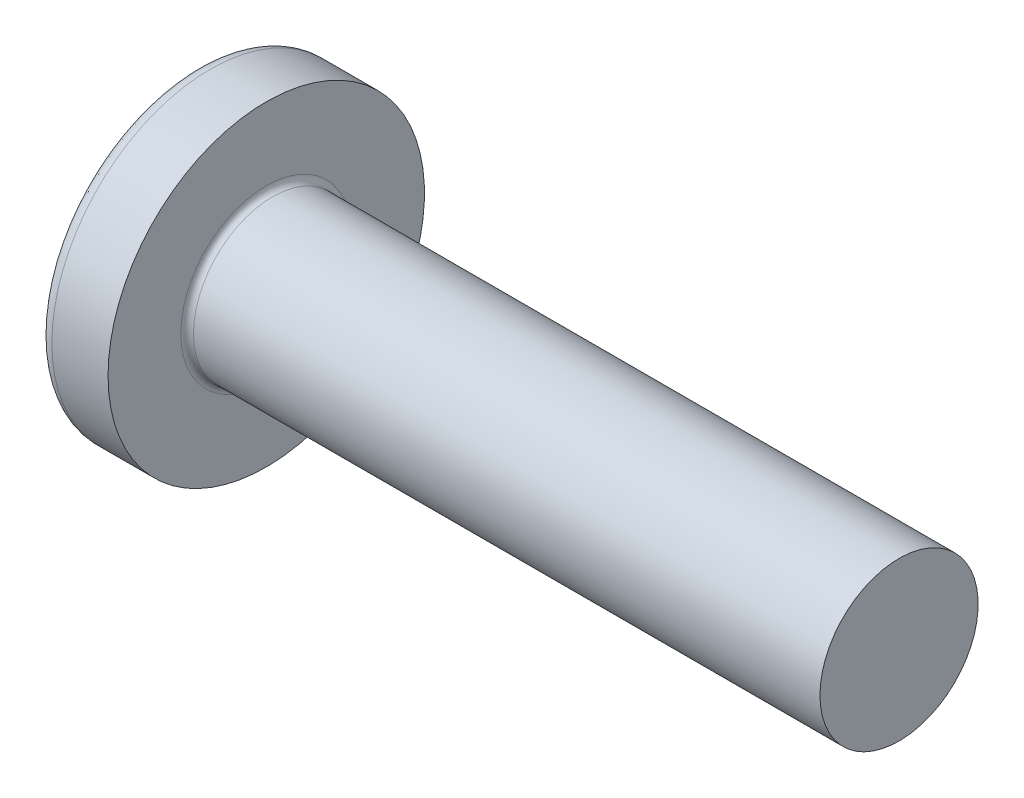
SolidWorks part; units mm, degrees
ref_plane "Plane1" through (0, 0, 0) normal (0, 0, 1) x (1, 0, 0)
ref_plane "Plane2" through (0, 0, 0) normal (0, 1, 0) x (1, 0, 0)
ref_plane "Plane3" through (0, 0, 0) normal (1, 0, 0) x (0, 0, -1)
sketch "BodySke" plane through (0, 0, 0) normal (0, 0, 1) x (1, 0, 0)
  line L0 (7.5, 5) -> (7.5, 10)
  line L1 (8.25, 6.35) -> (8.25, -3.175) construction
  line L2 (-25.4, 0) -> (127, 0) construction
  line L3 (47.5, 0) -> (0, 0)
  line L4 (7.5, 5) -> (47.5, 5)
  line L5 (47.5, 5) -> (47.5, 0)
  line L6 (3.9501, 10) -> (7.5, 10)
  line L8 (7.5, 6.35) -> (7.5, -3.175) construction
  arc A0 (3.2319, 9.6424) -> (0, 0) centre (16, 0) ccw
  arc A2 (3.2319, 9.6424) -> (3.9501, 10) centre (3.9501, 9.1) cw
  dimension "Head_fillet_rad" = 0.9
  dimension "Head_crown_rad" = 16
  dimension "Head_ht" = 7.5
  dimension "Diameter" = 10
  dimension "Length" = 40
  dimension "Head_dia" = 20
  dimension "Advance" = 1.5
  dimension "Thread_nom" = 40
revolve "Base-Revolve" add sketch "BodySke"
cosmetic thread "ThreadCosmetic"
fillet "Fillet1" radius 0.4 1 edges at (7.5, 0, 5)
sketch "Sketch3" plane through (0, 0, 0) normal (1, 0, 0) x (0, 0, -1)
  line L0 (1.08, -4.95) -> (-1.08, -4.95)
  line L1 (1.08, -4.95) -> (1.08, 4.95)
  line L2 (-1.08, 4.95) -> (1.08, 4.95)
  line L3 (-1.08, 4.95) -> (-1.08, -4.95)
  dimension "D1" = 4.95
  dimension "Cross_dia" = 9.9
  dimension "D2" = 1.08
  dimension "Cross_width" = 2.16
ref_plane "Plane4" through (5.69, 0, 0) normal (1, 0, 0) x (0, 0, -1)
sketch "Sketch4" plane through (5.69, 0, 0) normal (1, 0, 0) x (0, 0, -1)
  line L0 (1.08, -2.1131) -> (-1.08, -2.1131)
  line L1 (1.08, -2.1131) -> (1.08, 2.1131)
  line L2 (-1.08, 2.1131) -> (1.08, 2.1131)
  line L3 (-1.08, 2.1131) -> (-1.08, -2.1131)
  dimension "D1" = 2.16
  dimension "D2" = 4.2261
  dimension "D3" = 1.08
  dimension "D4" = 2.1131
loft "Recess" cut profiles "Sketch3", "Sketch4"
pattern_circular "RecPat" count 2 every 90 about axis through (0, 0, 0) along (1, 0, 0) of "Recess"
sketch "RecCorSke" plane through (0, 0, 0) normal (0, 0, 1) x (1, 0, 0)
  line L0 (-3.175, 0) -> (15.875, 0) construction
  line L1 (-25.4, 0) -> (127, 0) construction
  line L2 (0, 0) -> (0, 2.3284)
  line L3 (0, 2.3284) -> (5.69, 1.9305)
  line L4 (5.69, 1.9305) -> (6.3173, 0)
  line L5 (6.3173, 0) -> (0, 0)
  dimension "Diameter" = 3.861
  dimension "Depth" = 5.69
  dimension "Draft_angle" = 4
  dimension "Bottom_angle" = 18
revolve "RecessCore" cut sketch "RecCorSke" angle 360 about L0
sketch "ThdSchSke" plane through (0, 0, 0) normal (0, 0, 1) x (1, 0, 0)
  line L0 (10.5, -4.172) -> (9.9202, -5)
  line L1 (10.5, -4.172) -> (11.0798, -5)
  line L2 (11.0798, -5) -> (11.0798, -6.25)
  line L3 (-3.175, 0) -> (5.1513, 0) construction
  line L5 (11.0798, -6.25) -> (9.9202, -6.25)
  line L6 (9.9202, -6.25) -> (9.9202, -5)
  dimension "Thread_minor" = 8.344
  dimension "Diameter" = 10
  dimension "Start" = 10.5
  dimension "SideAngle" = 55
  dimension "VeeAngle" = 70
  dimension "Overcut" = 12.5
revolve "ThreadSchematic" [suppressed] cut sketch "ThdSchSke" angle 360 about L3
pattern_linear "ThdSchPat" [suppressed]
equation "\"D1@Sketch3\" = \"Cross_dia@Sketch3\" / 2"
equation "\"D2@Sketch3\" = \"Cross_width@Sketch3\" / 2"
equation "\"Depth@RecCorSke\" = \"Cross_depth@Plane4\""
equation "\"D1@Sketch4\" = \"Cross_width@Sketch3\""
equation "\"D2@Sketch4\" = \"Cross_dia@Sketch3\" - 2.0 * \"Cross_depth@Plane4\" * tan(26.5  * 0.017453292)"
equation "\"D3@Sketch4\" = \"D1@Sketch4\" / 2"
equation "\"D4@Sketch4\" = \"D2@Sketch4\" / 2"
equation "\"Thread_length@ThreadCosmetic\" = ((sgn( (\"Length@BodySke\" - \"Advance@BodySke\" * 2.0 ) - \"Thread_nom@BodySke\" )-1)*( (\"Length@BodySke\" - \"Advance@BodySke\" * 2.0 ) - \"Thread_nom@BodySke\" ))/-2+ \"Thread_nom@BodySke\""
equation "\"Thread_minor@ThdSchSke\" = \"Thread_minor@ThreadCosmetic\""
equation "\"Diameter@ThdSchSke\" = \"Diameter@BodySke\""
equation "\"Overcut@ThdSchSke\" = \"Diameter@BodySke\" * 1.25"
equation "\"Start@ThdSchSke\" = \"Head_ht@BodySke\" + \"Length@BodySke\" - \"Thread_length@ThreadCosmetic\"  '---Non-countersunk---"
equation "\"Num_threads@ThdSchPat\" = int( \"Thread_length@ThreadCosmetic\" / \"Advance@BodySke\" + 0.999 )  + 1"
equation "\"Advance@ThdSchPat\" = \"Thread_length@ThreadCosmetic\" /  (\"Num_threads@ThdSchPat\" - 1) 'relax it"
